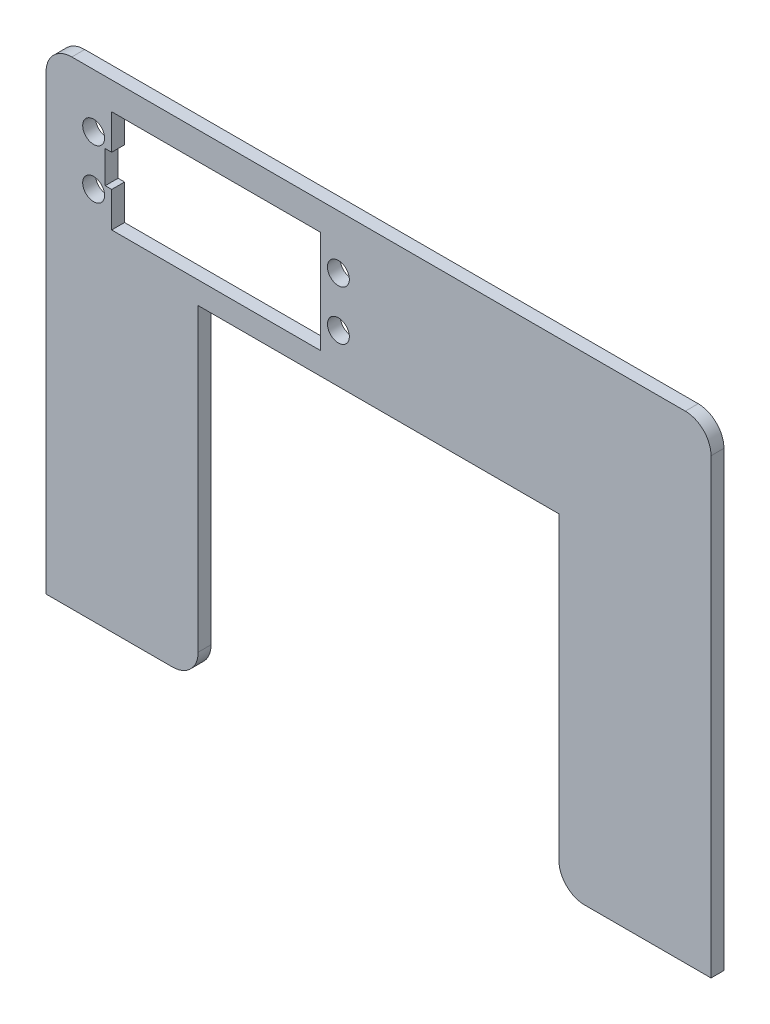
SolidWorks part; units mm, degrees
ref_plane "Front Plane" through (0, 0, 0) normal (0, 0, 1) x (1, 0, 0)
ref_plane "Top Plane" through (0, 0, 0) normal (0, 1, 0) x (1, 0, 0)
ref_plane "Right Plane" through (0, 0, 0) normal (1, 0, 0) x (0, 0, -1)
sketch "Sketch1" plane through (0, 0, 0) normal (0, 0, 1) x (1, 0, 0)
  line L0 (35.56, -47.131) -> (35.56, 17.131)
  line L1 (65.56, -47.131) -> (35.56, -47.131)
  line L2 (65.56, -47.131) -> (65.56, 47.131)
  line L3 (65.56, 47.131) -> (-65.56, 47.131)
  line L4 (-65.56, -47.131) -> (-65.56, 47.131)
  line L5 (65.56, -47.131) -> (-65.56, 47.131) construction
  line L6 (65.56, 47.131) -> (-65.56, -47.131) construction
  line L7 (35.56, 17.131) -> (-35.56, 17.131)
  line L8 (-35.56, 17.131) -> (-35.56, -47.131)
  line L9 (-35.56, -47.131) -> (-65.56, -47.131)
  line L10 (0, 0) -> (0, 47.131) construction
  point P0 (0, 0)
  dimension "D1" = 71.12
  dimension "D2" = 64.262
  dimension "D3" = 30
  dimension "D4" = 30
extrude "Boss-Extrude1" add sketch "Sketch1" along normal blind 2.54
sketch "Sketch2" plane through (0, 0, 2.54) normal (0, 0, 1) x (1, 0, 0)
  line L0 (-40.56, 41.7055) -> (-40.56, 21.5125) construction
  line L1 (-11.477, 41.7055) -> (-52.625, 41.7055)
  line L2 (-11.477, 41.7055) -> (-11.477, 31.609)
  line L3 (-11.477, 21.5125) -> (-52.625, 21.5125)
  line L4 (-52.625, 41.7055) -> (-52.625, 21.5125)
  line L5 (-11.477, 41.7055) -> (-52.625, 21.5125) construction
  line L6 (-11.477, 21.5125) -> (-52.625, 41.7055) construction
  line L8 (-52.625, 31.609) -> (-11.477, 31.609) construction
  line L9 (-65.56, -47.131) -> (-35.56, -47.131) construction
  line L10 (-32.051, 41.7055) -> (-32.051, 21.5125) construction
  line L11 (-56.181, 36.4985) -> (-56.181, 26.7195) construction
  line L12 (-7.921, 26.7195) -> (-7.921, 36.4985) construction
  line L13 (-56.181, 36.4985) -> (-7.921, 36.4985) construction
  line L14 (-35.56, -47.131) -> (-35.56, 17.131) construction
  line L18 (-11.477, 31.609) -> (-11.477, 21.5125)
  circle A0 centre (-56.181, 36.4985) radius 2.159
  circle A1 centre (-56.181, 26.7195) radius 2.159
  circle A2 centre (-7.921, 36.4985) radius 2.159
  circle A3 centre (-7.921, 26.7195) radius 2.159
  point P0 (-32.051, 31.609)
  point P24 (0, 0)
  point P25 (-11.477, 31.609)
  point P26 (0, 0)
  dimension "D6" = 4.318
  dimension "D1" = 41.148
  dimension "D2" = 20.193
  dimension "D3" = 12.065
  dimension "D4" = 78.74
  dimension "D5" = 48.26
  dimension "D7" = 9.779
  dimension "D8" = 5
extrude "Cut-Extrude1" cut sketch "Sketch2" against normal blind 2.54
fillet "Fillet1" radius 5.08 4 edges at (35.56, -47.131, 1.27) (-35.56, -47.131, 1.27) (65.56, 47.131, 1.27) (-65.56, 47.131, 1.27)
sketch "Sketch3" plane through (0, 0, 2.54) normal (0, 0, 1) x (1, 0, 0)
  line L0 (-52.625, 41.7055) -> (-52.625, 21.5125) construction
  line L1 (-51.355, 28.434) -> (-53.895, 28.434)
  line L2 (-51.355, 28.434) -> (-51.355, 34.784)
  line L3 (-51.355, 34.784) -> (-53.895, 34.784)
  line L4 (-53.895, 28.434) -> (-53.895, 34.784)
  line L5 (-51.355, 28.434) -> (-53.895, 34.784) construction
  line L6 (-51.355, 34.784) -> (-53.895, 28.434) construction
  point P0 (-52.625, 31.609)
  dimension "D1" = 2.54
  dimension "D2" = 6.35
extrude "Cut-Extrude4" cut sketch "Sketch3" against normal through all
